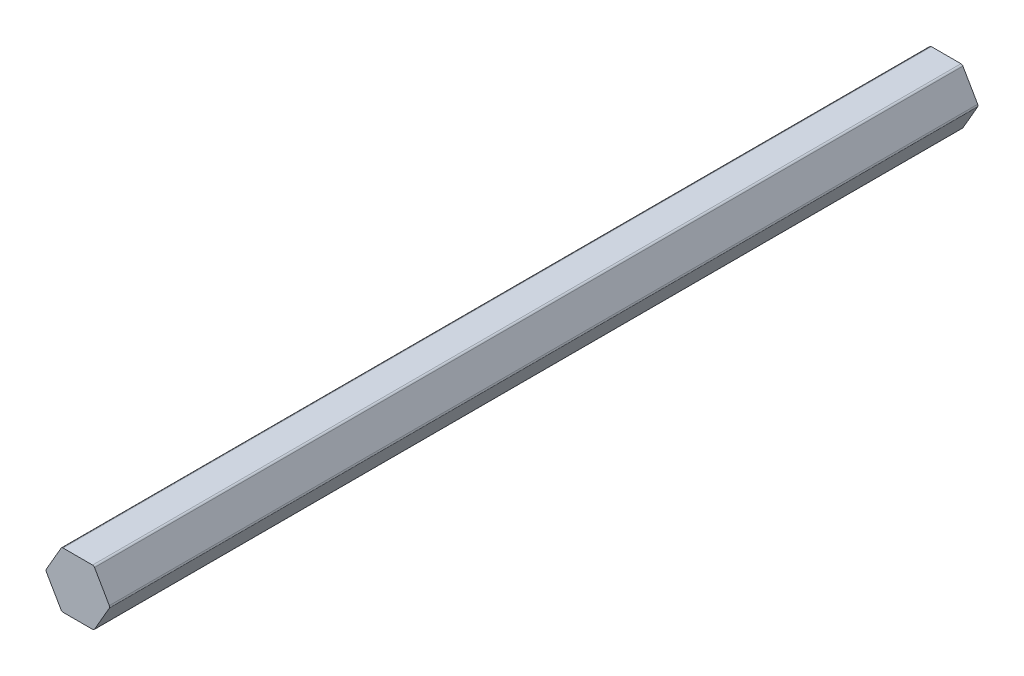
SolidWorks part; units mm, degrees
ref_plane "Front Plane" through (0, 0, 0) normal (0, 0, 1) x (1, 0, 0)
ref_plane "Top Plane" through (0, 0, 0) normal (0, 1, 0) x (1, 0, 0)
ref_plane "Right Plane" through (0, 0, 0) normal (1, 0, 0) x (0, 0, -1)
ref_plane "Plane1" through (0, 0, -228.6) normal (0, 0, -1) x (-1, 0, 0)
sketch "Sketch1" plane through (0, 0, -228.6) normal (0, 0, -1) x (-1, 0, 0)
  line L0 (3.8055, -6.0833) -> (7.171, -0.254)
  line L1 (7.171, 0.254) -> (3.8055, 6.0833)
  line L2 (3.3655, 6.3373) -> (-3.3655, 6.3373)
  line L3 (-3.8055, 6.0833) -> (-7.171, 0.254)
  line L4 (-7.171, -0.254) -> (-3.8055, -6.0833)
  line L5 (-3.3655, -6.3373) -> (3.3655, -6.3373)
  arc A0 (3.3655, -6.3373) -> (3.8055, -6.0833) centre (3.3655, -5.8293) ccw
  arc A1 (7.171, -0.254) -> (7.171, 0.254) centre (6.7311, 0) ccw
  arc A2 (3.8055, 6.0833) -> (3.3655, 6.3373) centre (3.3655, 5.8293) ccw
  arc A3 (-3.3655, 6.3373) -> (-3.8055, 6.0833) centre (-3.3655, 5.8293) ccw
  arc A4 (-7.171, 0.254) -> (-7.171, -0.254) centre (-6.7311, 0) ccw
  arc A5 (-3.8055, -6.0833) -> (-3.3655, -6.3373) centre (-3.3655, -5.8293) ccw
  dimension "D1" = 0.508
  dimension "D2" = 3.3655
  dimension "D3" = 3.3655
  dimension "D4" = 3.8055
  dimension "D5" = 6.7311
  dimension "D6" = 0.254
extrude "Boss-Extrude1" add sketch "Sketch1" against normal blind 197.612
